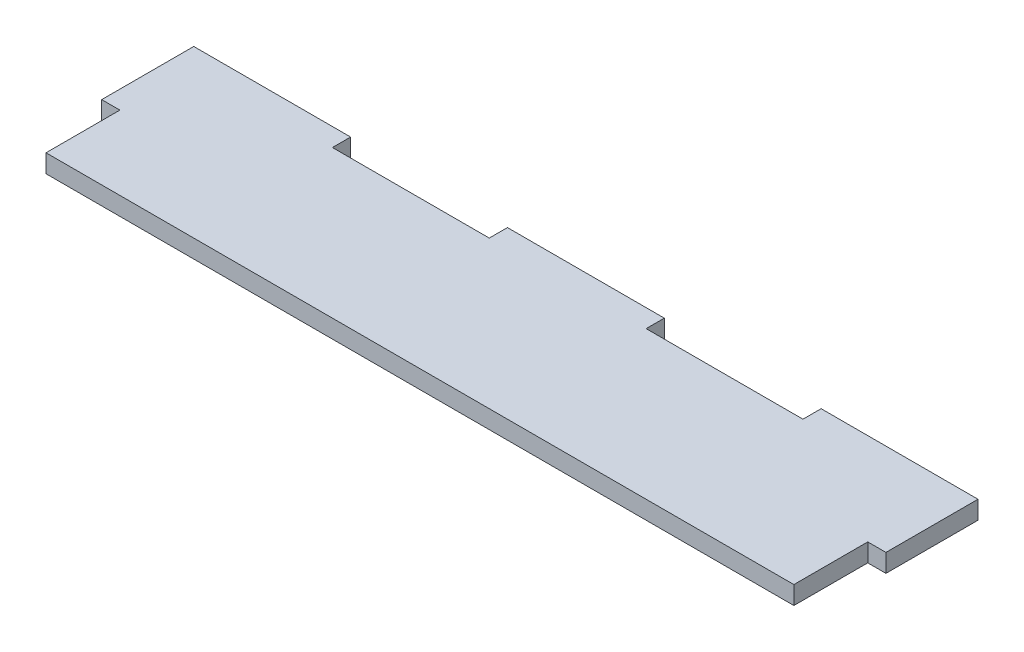
SolidWorks part; units mm, degrees
material "A-Glass Fiber"
ref_plane "Front Plane" through (0, 0, 0) normal (0, 0, 1) x (1, 0, 0)
ref_plane "Top Plane" through (0, 0, 0) normal (0, 1, 0) x (1, 0, 0)
ref_plane "Right Plane" through (0, 0, 0) normal (1, 0, 0) x (0, 0, -1)
sketch "Sketch1" plane through (0, 0, 0) normal (0, 1, 0) x (1, 0, 0)
  line L9 (0, 0) -> (438.15, 0)
  line L10 (0, 0) -> (0, -92.71)
  line L11 (0, -92.71) -> (438.15, -92.71)
  line L12 (438.15, 0) -> (438.15, -92.71)
  line L13 (0, 0) -> (87.63, 0)
  line L14 (0, 0) -> (0, -10.16)
  line L15 (0, -10.16) -> (87.63, -10.16)
  line L16 (87.63, 0) -> (87.63, -10.16)
  line L17 (87.63, -10.16) -> (175.26, -10.16)
  line L18 (87.63, -10.16) -> (87.63, 0)
  line L19 (87.63, 0) -> (175.26, 0)
  line L20 (175.26, -10.16) -> (175.26, 0)
  line L21 (175.26, 0) -> (262.89, 0)
  line L22 (175.26, 0) -> (175.26, -10.16)
  line L23 (175.26, -10.16) -> (262.89, -10.16)
  line L24 (262.89, 0) -> (262.89, -10.16)
  line L25 (262.89, -10.16) -> (350.52, -10.16)
  line L26 (262.89, -10.16) -> (262.89, 0)
  line L27 (262.89, 0) -> (350.52, 0)
  line L28 (350.52, -10.16) -> (350.52, 0)
  line L29 (350.52, 0) -> (438.15, 0)
  line L30 (350.52, 0) -> (350.52, -10.16)
  line L31 (350.52, -10.16) -> (438.15, -10.16)
  line L32 (438.15, 0) -> (438.15, -10.16)
  line L33 (0, -10.16) -> (10.16, -10.16)
  line L34 (0, -10.16) -> (0, -51.435)
  line L35 (0, -51.435) -> (10.16, -51.435)
  line L36 (10.16, -10.16) -> (10.16, -51.435)
  line L37 (10.16, -51.435) -> (0, -51.435)
  line L38 (10.16, -51.435) -> (10.16, -92.71)
  line L39 (10.16, -92.71) -> (0, -92.71)
  line L40 (0, -51.435) -> (0, -92.71)
  line L41 (438.15, -10.16) -> (427.99, -10.16)
  line L42 (438.15, -10.16) -> (438.15, -51.435)
  line L43 (438.15, -51.435) -> (427.99, -51.435)
  line L44 (427.99, -10.16) -> (427.99, -51.435)
  line L45 (427.99, -51.435) -> (438.15, -51.435)
  line L46 (427.99, -51.435) -> (427.99, -92.71)
  line L47 (427.99, -92.71) -> (438.15, -92.71)
  line L48 (438.15, -51.435) -> (438.15, -92.71)
  dimension "D1" = 438.15
  dimension "D2" = 92.71
  dimension "D3" = 10.16
  dimension "D4" = 10.16
  dimension "D5" = 10.16
extrude "Boss-Extrude1" add sketch "Sketch1" along normal blind 10.16 contours L31 L25 L23 L17 L15 L10 L11 L12 | L16 L9 L10 L15 | L24 L9 L20 L23 | L28 L31 L12 L9 | L31 L44 L43 L12 | L36 L15 L10 L35
